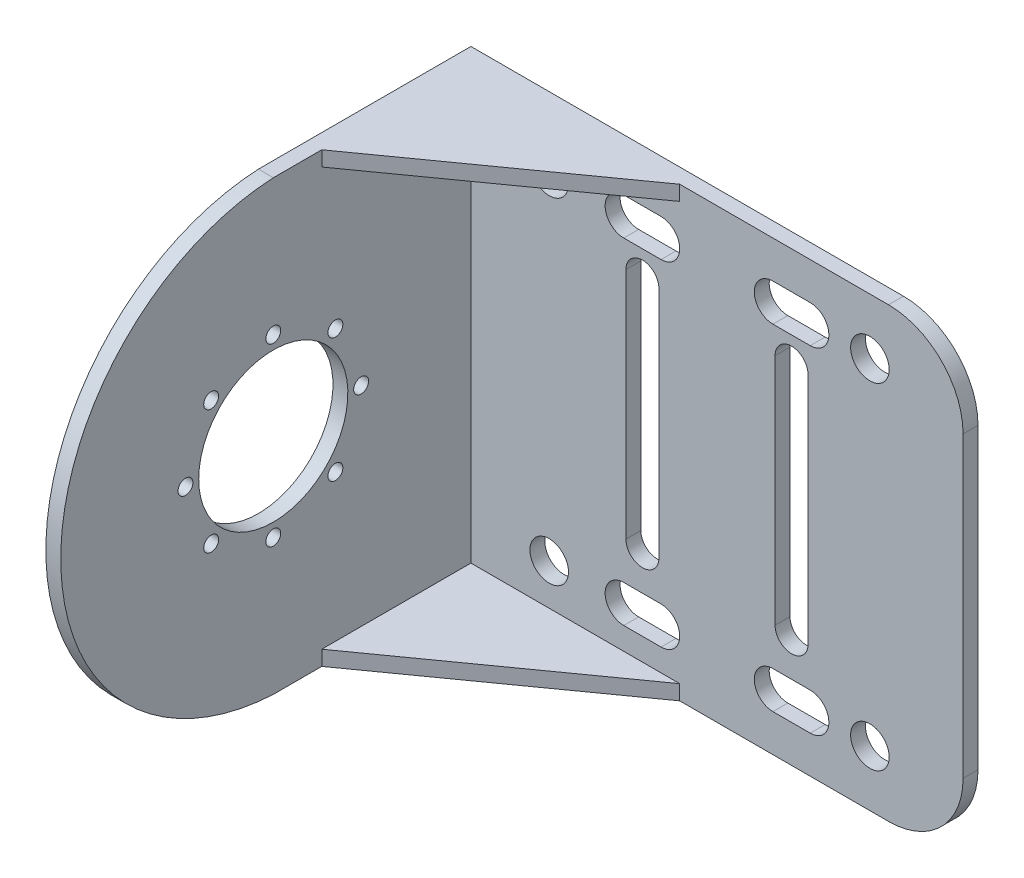
SolidWorks part; units mm, degrees
ref_plane "Front Plane" through (0, 0, 0) normal (0, 0, 1) x (1, 0, 0)
ref_plane "Top Plane" through (0, 0, 0) normal (0, 1, 0) x (1, 0, 0)
ref_plane "Right Plane" through (0, 0, 0) normal (1, 0, 0) x (0, 0, -1)
sketch "Sketch2" plane through (0, 0, 0) normal (0, 0, 1) x (1, 0, 0)
  line L1 (-34, -30) -> (24, -30)
  line L2 (-34, -30) -> (-34, 30)
  line L3 (-34, 30) -> (24, 30)
  line L4 (34, -20) -> (34, 20)
  line L5 (-34, -30) -> (34, 30) construction
  line L6 (-34, 30) -> (34, -30) construction
  arc A0 (34, -20) -> (24, -30) centre (24, -20) cw
  arc A1 (34, 20) -> (24, 30) centre (24, 20) ccw
  point P0 (0, 0)
  dimension "D3" = 10
  dimension "D1" = 68
  dimension "D2" = 60
extrude "Boss-Extrude1" add sketch "Sketch2" along normal blind 2
sketch "Sketch4" plane through (0, 0, 2) normal (0, 0, 1) x (1, 0, 0)
  line L1 (-34, -30) -> (-4, -30)
  line L2 (-34, -30) -> (-34, -28)
  line L3 (-34, -28) -> (-4, -28)
  line L4 (-4, -30) -> (-4, -28)
  line L5 (-34, 30) -> (-4, 30)
  line L6 (-34, 30) -> (-34, 28)
  line L7 (-34, 28) -> (-4, 28)
  line L8 (-4, 30) -> (-4, 28)
  dimension "D1" = 30
  dimension "D2" = 2
  dimension "D3" = 30
  dimension "D4" = 2
sketch "Sketch5" plane through (0, 0, 2) normal (0, 0, 1) x (1, 0, 0)
  line L0 (-34, -30) -> (-4, -30) construction
  line L1 (-34, 30) -> (-32, 30)
  line L2 (-34, 30) -> (-34, -30)
  line L3 (-34, -30) -> (-32, -30)
  line L4 (-32, 30) -> (-32, -30)
  dimension "D1" = 2
extrude "Boss-Extrude2" add sketch "Sketch5" along normal blind 55
sketch "Sketch6" plane through (-34, 0, 0) normal (-1, 0, 0) x (0, 0, 1)
  line L0 (57, 0) -> (0, 0) construction
  line L1 (57, 30) -> (57, -30) construction
  line L2 (28.5, 30) -> (28.5, -30) construction
  line L3 (57, 30) -> (0, 30) construction
  line L4 (57, -30) -> (0, -30) construction
  circle A0 centre (28.5, 0) radius 10
  arc A1 (28.5, 30) -> (28.5, -30) centre (26.9605, 0) cw
  circle A2 centre (40.2779, 0) radius 1
  circle A3 centre (36.8282, -8.3282) radius 1
  circle A4 centre (28.5, -11.7779) radius 1
  circle A5 centre (20.1718, -8.3282) radius 1
  circle A6 centre (16.7221, 0) radius 1
  circle A7 centre (20.1718, 8.3282) radius 1
  circle A8 centre (28.5, 11.7779) radius 1
  circle A9 centre (36.8282, 8.3282) radius 1
  point P14 (28.5, 0)
  point P15 (57, 0)
  line M3 (0, -30) -> (57, -30)
  line M4 (57, -30) -> (57, 30)
  line M5 (57, 30) -> (0, 30)
  dimension "D1" = 8
extrude "Cut-Extrude2" cut sketch "Sketch6" against normal blind 55 contours A0 | A2 | A3 | A4 | A5 | A6 | A7 | A8 | A9 | A1 M5 M4 | A1 M4 M3
sketch "Sketch8" plane through (0, 0, 2) normal (0, 0, 1) x (1, 0, 0)
  line L0 (-11.5, 22.5) -> (-6.5, 22.5) construction
  line L1 (-11.5, 25) -> (-6.5, 25)
  line L2 (-11.5, 20) -> (-6.5, 20)
  line L3 (8.5, 22.5) -> (13.5, 22.5) construction
  line L4 (8.5, 25) -> (13.5, 25)
  line L5 (8.5, 20) -> (13.5, 20)
  line L7 (-13.5267, 0) -> (11, 0) construction
  line L8 (8.5, -22.5) -> (13.5, -22.5) construction
  line L9 (8.5, -25) -> (13.5, -25)
  line L10 (8.5, -20) -> (13.5, -20)
  line L11 (-11.5, -22.5) -> (-6.5, -22.5) construction
  line L12 (-11.5, -25) -> (-6.5, -25)
  line L13 (-11.5, -20) -> (-6.5, -20)
  line L14 (-9, 16.4814) -> (-9, -14.8194) construction
  line L15 (-6.7865, 16.4814) -> (-6.7865, -14.8194)
  line L16 (-11.2135, 16.4814) -> (-11.2135, -14.8194)
  line L17 (11, 16.4814) -> (11, -14.8194) construction
  line L18 (13.2135, 16.4814) -> (13.2135, -14.8194)
  line L19 (8.7865, 16.4814) -> (8.7865, -14.8194)
  circle A0 centre (-21.5, 22.5) radius 2.5853
  circle A1 centre (-21.5, -22.5) radius 2.5853
  circle A2 centre (21.5, 22.5) radius 2.5853
  circle A3 centre (21.5, -22.5) radius 2.5853
  arc A4 (-11.5, 25) -> (-11.5, 20) centre (-11.5, 22.5) ccw
  arc A5 (-6.5, 20) -> (-6.5, 25) centre (-6.5, 22.5) ccw
  arc A6 (8.5, 25) -> (8.5, 20) centre (8.5, 22.5) ccw
  arc A7 (13.5, 20) -> (13.5, 25) centre (13.5, 22.5) ccw
  arc A8 (8.5, -25) -> (8.5, -20) centre (8.5, -22.5) cw
  arc A9 (13.5, -20) -> (13.5, -25) centre (13.5, -22.5) cw
  arc A10 (-11.5, -25) -> (-11.5, -20) centre (-11.5, -22.5) cw
  arc A11 (-6.5, -20) -> (-6.5, -25) centre (-6.5, -22.5) cw
  arc A12 (-6.7865, 16.4814) -> (-11.2135, 16.4814) centre (-9, 16.4814) ccw
  arc A13 (-11.2135, -14.8194) -> (-6.7865, -14.8194) centre (-9, -14.8194) ccw
  arc A14 (13.2135, 16.4814) -> (8.7865, 16.4814) centre (11, 16.4814) ccw
  arc A15 (8.7865, -14.8194) -> (13.2135, -14.8194) centre (11, -14.8194) ccw
  point P8 (-9, 22.5)
  point P16 (11, 22.5)
  point P27 (11, -22.5)
  point P34 (-9, -22.5)
  point P41 (-9, 0.831)
  point P48 (11, 0.831)
  dimension "D3" = 43
  dimension "D5" = 2.5
  dimension "D1" = 45
  dimension "D2" = 22.5
  dimension "D4" = 21.5
  dimension "D6" = 5
  dimension "D7" = 12.5
  dimension "D8" = 10.5
extrude "Cut-Extrude3" cut sketch "Sketch8" against normal blind 55 contours A0 | L2 A5 L1 A4 | L5 A7 L4 A6 | A2 | L19 A15 L18 A14 | L16 A13 L15 A12 | A1 | A11 L13 A10 L12 | A9 L10 A8 L9 | A3
extrude "Boss-Extrude3" add sketch "Sketch4" along normal blind 20
sketch "Sketch10" plane through (0, -30, 0) normal (0, -1, 0) x (1, 0, 0)
  line L0 (-32, 22) -> (-4, 2)
  line L1 (-4, 2) -> (-4, 22)
  line L2 (-4, 22) -> (-32, 22)
extrude "Cut-Extrude4" cut sketch "Sketch10" against normal blind 100
